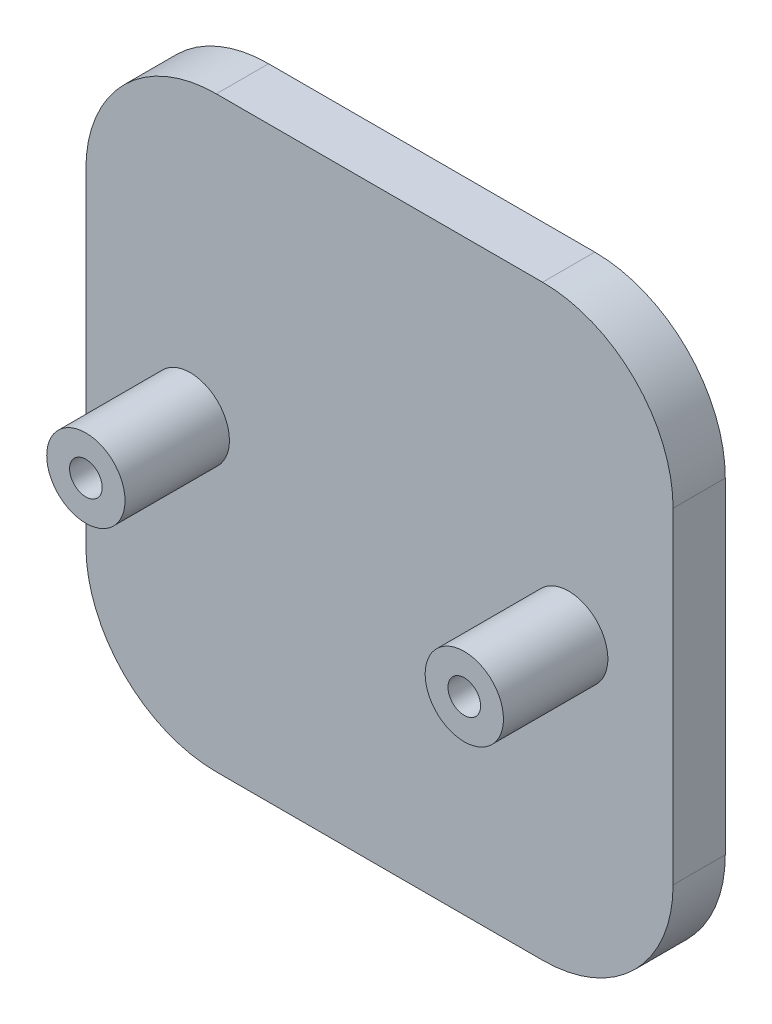
SolidWorks part; units mm, degrees
ref_plane "Front Plane" through (0, 0, 0) normal (0, 0, 1) x (1, 0, 0)
ref_plane "Top Plane" through (0, 0, 0) normal (0, 1, 0) x (1, 0, 0)
ref_plane "Right Plane" through (0, 0, 0) normal (1, 0, 0) x (0, 0, -1)
sketch "Sketch5" plane through (0, 0, 0) normal (0, 0, 1) x (1, 0, 0)
  line L1 (-22.5, -22.5) -> (22.5, -22.5)
  line L2 (-22.5, -22.5) -> (-22.5, 22.5)
  line L3 (-22.5, 22.5) -> (22.5, 22.5)
  line L4 (22.5, -22.5) -> (22.5, 22.5)
  line L5 (-22.5, -22.5) -> (22.5, 22.5) construction
  line L6 (-22.5, 22.5) -> (22.5, -22.5) construction
  point P0 (0, 0)
extrude "Boss-Extrude1" add sketch "Sketch5" along normal blind 4
sketch "Sketch7" plane through (0, 0, 4) normal (0, 0, 1) x (1, 0, 0)
  line L5 (0, 0) -> (-14.5, 0) construction
  circle A1 centre (-14.5, 0) radius 3
extrude "Boss-Extrude2" add sketch "Sketch7" along normal blind 8 contours A1
sketch "Sketch9" plane through (0, 0, 4) normal (0, 0, 1) x (1, 0, 0)
  line L0 (0, 0) -> (14.5, 0) construction
  circle A0 centre (14.5, 0) radius 3
extrude "Boss-Extrude3" add sketch "Sketch9" along normal blind 8
hole_wizard "Tap Drill for M3x0.5 Tap1" positions "Sketch18" profile "Sketch19" hole size "M3x0.5" standard "ANSI Metric"
sketch "Sketch18" plane through (0, 0, 12) normal (0, 0, 1) x (1, 0, 0)
  point P0 (-14.5, 0)
sketch "Sketch19" plane through (-14.5, 0, 12) normal (1, 0, 0) x (0, -1, 0)
  line L0 (0, 0) -> (0, 8.7511)
  line L1 (0, 8.7511) -> (1.25, 8)
  line L2 (1.25, 8) -> (1.25, 0)
  line L5 (1.25, 0) -> (0, 0)
  line L10 (0, 8.7511) -> (-1.25, 8) construction
  line L11 (0, -6.35) -> (0, 107.95) construction
  dimension "Hole Dia." = 2.5
  dimension "Hole Depth" = 8
  dimension "Drill Angle" = 118
hole_wizard "Tap Drill for M3x0.5 Tap2" positions "Sketch20" profile "Sketch21" hole size "M3x0.5" standard "ANSI Metric"
sketch "Sketch20" plane through (0, 0, 12) normal (0, 0, 1) x (1, 0, 0)
  point P0 (14.5, 0)
  point P3 (14.5, 0)
sketch "Sketch21" plane through (14.5, 0, 12) normal (1, 0, 0) x (0, -1, 0)
  line L0 (0, 0) -> (0, 8.7511)
  line L1 (0, 8.7511) -> (1.25, 8)
  line L2 (1.25, 8) -> (1.25, 0)
  line L5 (1.25, 0) -> (0, 0)
  line L10 (0, 8.7511) -> (-1.25, 8) construction
  line L11 (0, -6.35) -> (0, 107.95) construction
  dimension "Hole Dia." = 2.5
  dimension "Hole Depth" = 8
  dimension "Drill Angle" = 118
fillet "Fillet3" radius 10 1 edges at (-22.5, 22.5, 2)
fillet "Fillet4" radius 10 3 edges at (-22.5, -22.5, 2) (22.5, -22.5, 2) (22.5, 22.5, 2)
